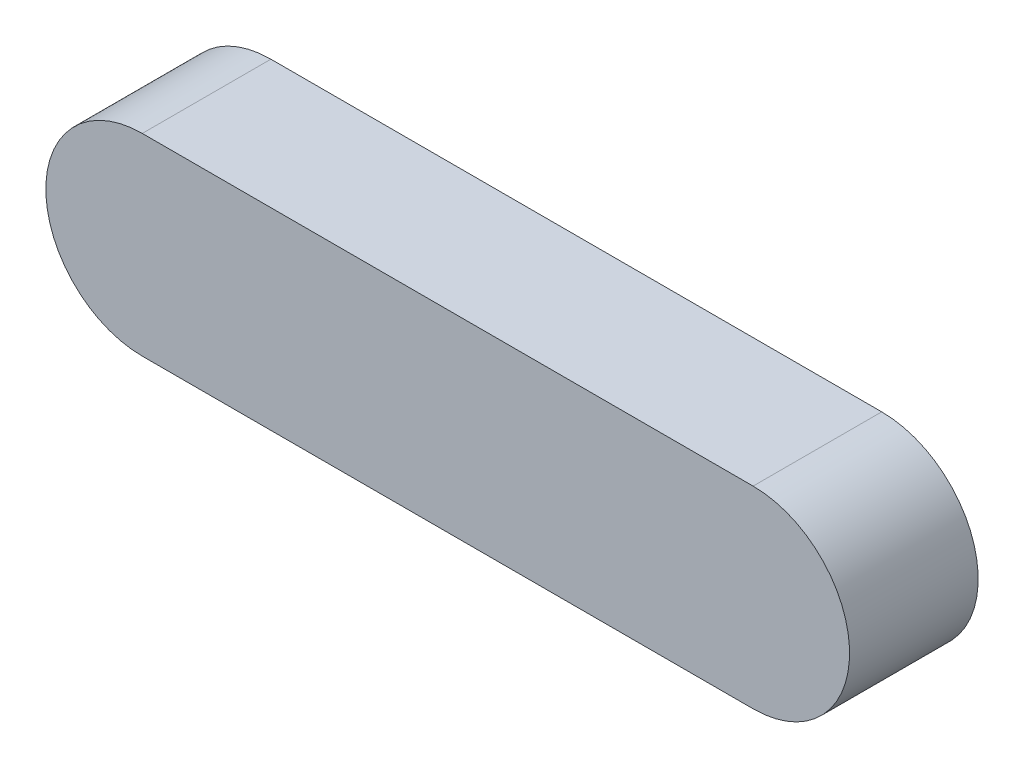
SolidWorks part; units mm, degrees
ref_plane "Front Plane" through (0, 0, 0) normal (0, 0, 1) x (1, 0, 0)
ref_plane "Top Plane" through (0, 0, 0) normal (0, 1, 0) x (1, 0, 0)
ref_plane "Right Plane" through (0, 0, 0) normal (1, 0, 0) x (0, 0, -1)
sketch "Sketch1" plane through (0, 0, 0) normal (0, 0, 1) x (1, 0, 0)
  line L0 (-19, 6) -> (0, 6)
  line L1 (0, 6) -> (0, -6)
  line L2 (0, -6) -> (-19, -6)
  arc A0 (-19, 6) -> (-19, -6) centre (-19, 0) ccw
  dimension "D1" = 12
  dimension "D2" = 19
  dimension "D3" = 6
extrude "Boss-Extrude1" add sketch "Sketch1" along normal blind 8
mirror "Mirror1" about plane through (0, 6, 8) normal (-1, 0, 0) of "Boss-Extrude1"
